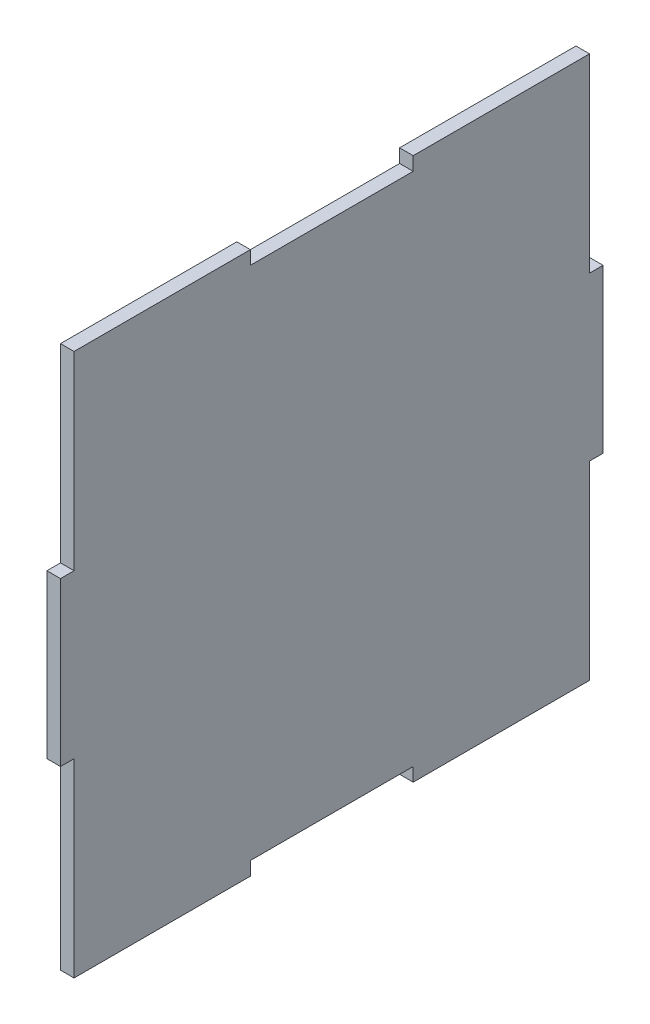
SolidWorks part; units mm, degrees
ref_plane "Front Plane" through (0, 0, 0) normal (0, 0, 1) x (1, 0, 0)
ref_plane "Top Plane" through (0, 0, 0) normal (0, 1, 0) x (1, 0, 0)
ref_plane "Right Plane" through (0, 0, 0) normal (1, 0, 0) x (0, 0, -1)
sketch "Sketch1" plane through (0, 0, 0) normal (1, 0, 0) x (0, 0, -1)
  line L0 (19.05, 63.5) -> (60.325, 63.5)
  line L1 (-60.325, -63.5) -> (-19.05, -63.5)
  line L2 (-63.5, -19.05) -> (-63.5, 19.05)
  line L3 (-60.325, 63.5) -> (-19.05, 63.5)
  line L4 (63.5, -19.05) -> (63.5, 19.05)
  line L5 (-63.5035, -63.5035) -> (63.5, 63.5) construction
  line L6 (-63.5, 63.5) -> (63.5, -63.5) construction
  line L8 (-19.05, 63.5) -> (-19.05, 60.325)
  line L9 (-19.05, 60.325) -> (19.05, 60.325)
  line L10 (19.05, 63.5) -> (19.05, 60.325)
  line L11 (60.325, 19.05) -> (60.325, -19.05) construction
  line L14 (63.5, 19.05) -> (60.325, 19.05)
  line L15 (60.325, 63.5) -> (60.325, 19.05)
  line L18 (63.5, -19.05) -> (60.325, -19.05)
  line L19 (60.325, -63.5) -> (60.325, -19.05)
  line L21 (-19.05, -63.5) -> (-19.05, -60.325)
  line L22 (-19.05, -60.325) -> (19.05, -60.325)
  line L23 (19.05, -63.5) -> (19.05, -60.325)
  line L26 (-63.5, -19.05) -> (-60.325, -19.05)
  line L27 (-60.325, -63.5) -> (-60.325, -19.05)
  line L30 (-63.5, 19.05) -> (-60.325, 19.05)
  line L31 (-60.325, 63.5) -> (-60.325, 19.05)
  line L32 (19.05, -63.5) -> (60.325, -63.5)
  point P0 (0, 0)
  point P10 (0, 60.325)
  point P27 (0, -60.325)
  point P28 (0, 0)
  point P29 (0, 0)
  point P30 (0, 0)
  dimension "D1" = 127
  dimension "D2" = 127
  dimension "D3" = 38.1
  dimension "D4" = 3.175
extrude "Boss-Extrude1" add sketch "Sketch1" along normal blind 3.175 contours L2 L30 L31 L3 L8 L9 L10 L0 L15 L14 L4 L18 L19 L32 L23 L22 L21 L1 L27 L26
